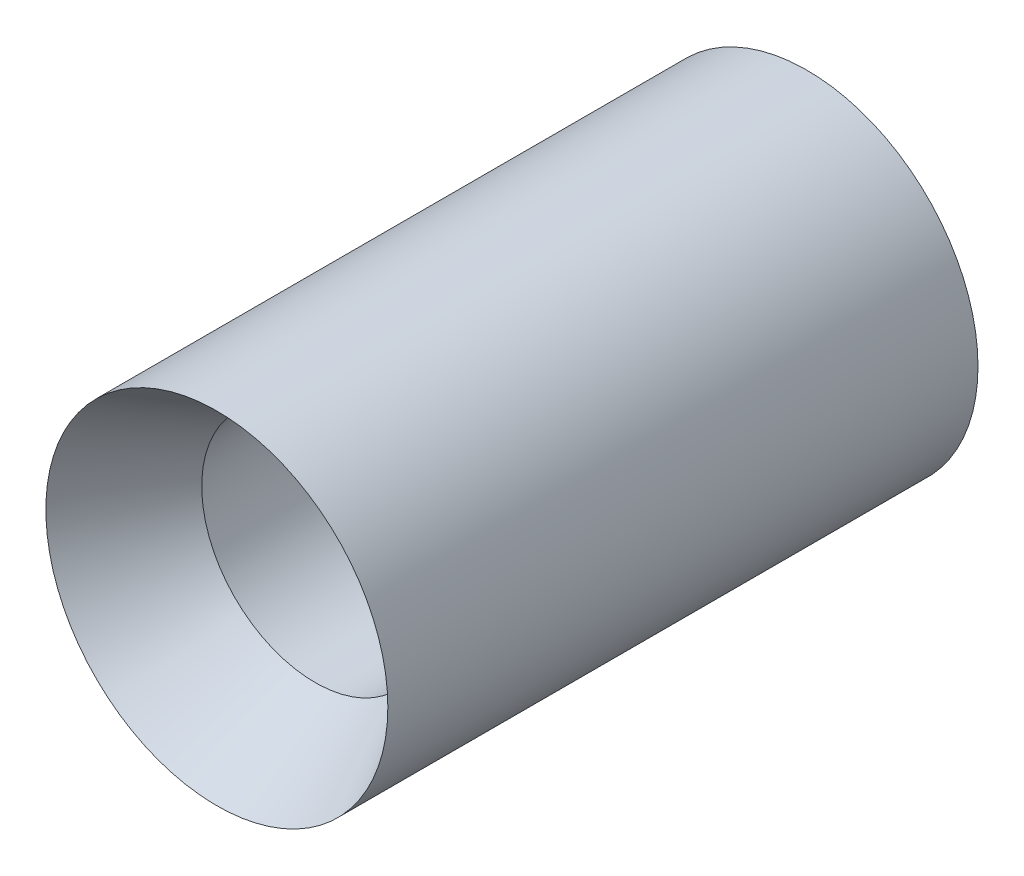
SolidWorks part; units mm, degrees
material "C (Graphite)"
ref_plane "Front Plane" through (0, 0, 0) normal (0, 0, 1) x (1, 0, 0)
ref_plane "Top Plane" through (0, 0, 0) normal (0, 1, 0) x (1, 0, 0)
ref_plane "Right Plane" through (0, 0, 0) normal (1, 0, 0) x (0, 0, -1)
sketch "Sketch3" plane through (0, 0, 0) normal (1, 0, 0) x (0, 0, -1)
  line L0 (0, 0) -> (77.1711, 0) construction
  line L3 (8.255, 9.525) -> (24.13, 9.525)
  line L4 (24.13, 9.525) -> (49.53, 12.7208)
  line L5 (49.53, 12.7208) -> (49.53, 14.351)
  line L6 (49.53, 14.351) -> (0, 14.351)
  line L7 (8.255, 9.525) -> (0, 14.351)
  point P3 (0, 0)
  dimension "D1" = 12.7208
  dimension "D2" = 9.525
  dimension "D3" = 8.255
  dimension "D4" = 49.53
  dimension "D6" = 15.875
  dimension "D7" = 14.351
revolve "Revolve1" add sketch "Sketch3" angle 360 about L0
